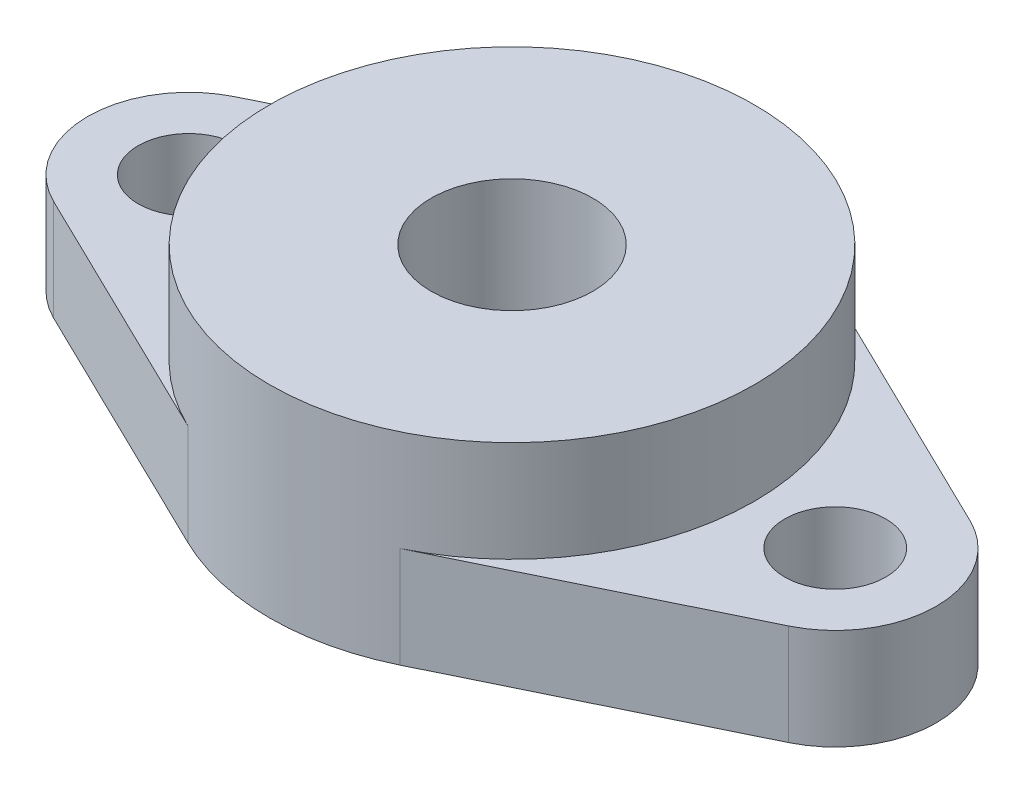
SolidWorks part; units mm, degrees
ref_plane "前视基准面" through (0, 0, 0) normal (0, 0, 1) x (1, 0, 0)
ref_plane "上视基准面" through (0, 0, 0) normal (0, 1, 0) x (1, 0, 0)
ref_plane "右视基准面" through (0, 0, 0) normal (1, 0, 0) x (0, 0, -1)
sketch "草图1" plane through (0, 0, 0) normal (0, 1, 0) x (1, 0, 0)
  line L0 (-5.25, 10.7906) -> (-18.1875, 4.4961)
  line L1 (-18.1875, -4.4961) -> (-5.25, -10.7906)
  line L2 (-16, 0) -> (0, 0) construction
  line L3 (0, 0) -> (0, 29.2225) construction
  line L4 (18.1875, -4.4961) -> (5.25, -10.7906)
  line L5 (5.25, 10.7906) -> (18.1875, 4.4961)
  arc A0 (-5.25, -10.7906) -> (5.25, -10.7906) centre (0, 0) ccw
  arc A1 (-18.1875, 4.4961) -> (-18.1875, -4.4961) centre (-16, 0) ccw
  arc A2 (18.1875, 4.4961) -> (18.1875, -4.4961) centre (16, 0) cw
  arc A3 (5.25, 10.7906) -> (-5.25, 10.7906) centre (0, 0) ccw
  dimension "D1" = 24
  dimension "D2" = 5
  dimension "D3" = 32
extrude "凸台-拉伸1" add sketch "草图1" along normal blind 5
sketch "草图3" plane through (0, 5, 0) normal (0, 1, 0) x (1, 0, 0)
  circle A0 centre (0, 0) radius 12
  dimension "D1" = 24
extrude "凸台-拉伸2" add sketch "草图3" along normal blind 5
sketch "草图4" plane through (0, 10, 0) normal (0, 1, 0) x (1, 0, 0)
  circle A0 centre (0, 0) radius 4
  dimension "D1" = 8
extrude "切除-拉伸1" cut sketch "草图4" against normal through all
sketch "草图6" plane through (0, 0, 0) normal (0, -1, 0) x (1, 0, 0)
  circle A0 centre (-16, 0) radius 2.5
  circle A1 centre (16, 0) radius 2.5
  dimension "D1" = 5
  dimension "D2" = 5
extrude "切除-拉伸2" cut sketch "草图6" against normal through all
